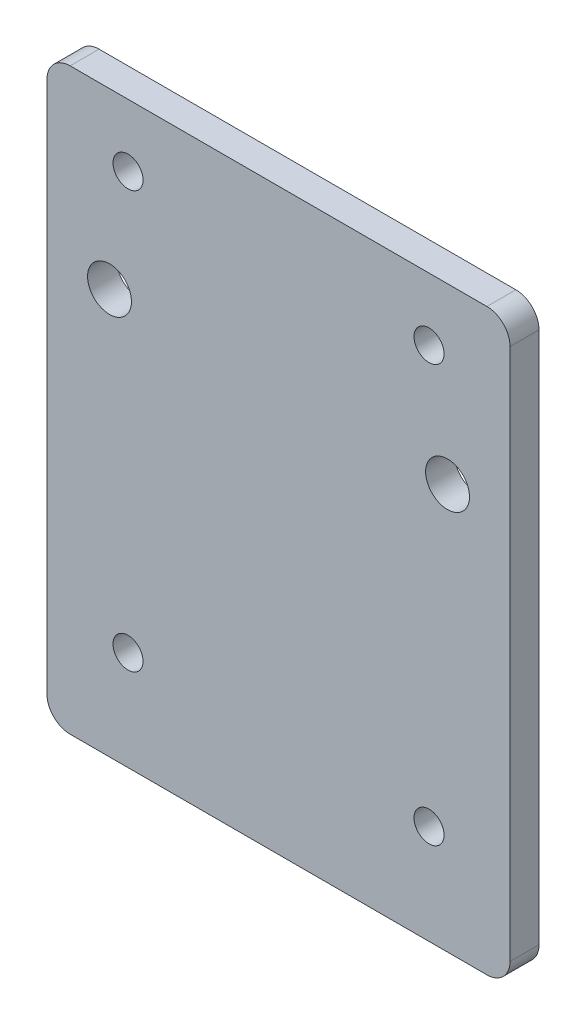
SolidWorks part; units mm, degrees
ref_plane "Front Plane" through (0, 0, 0) normal (0, 0, 1) x (1, 0, 0)
ref_plane "Top Plane" through (0, 0, 0) normal (0, 1, 0) x (1, 0, 0)
ref_plane "Right Plane" through (0, 0, 0) normal (1, 0, 0) x (0, 0, -1)
sketch "Sketch1" plane through (0, 0, 0) normal (0, 0, 1) x (1, 0, 0)
  line L1 (-25.4, 31.75) -> (25.4, 31.75)
  line L2 (-25.4, 31.75) -> (-25.4, -31.75)
  line L3 (-25.4, -31.75) -> (25.4, -31.75)
  line L4 (25.4, 31.75) -> (25.4, -31.75)
  line L5 (-25.4, 31.75) -> (25.4, -31.75) construction
  line L6 (-25.4, -31.75) -> (25.4, 31.75) construction
  point P0 (0, 0)
  dimension "D1" = 63.5
  dimension "D2" = 50.8
extrude "Boss-Extrude1" add sketch "Sketch1" along normal blind 3.175
hole_wizard "#10 (0.1935) Diameter Hole1" positions "Sketch2" profile "Sketch3" hole size "#10" standard "ANSI Inch" end condition up to next
sketch "Sketch2" plane through (0, 0, 0) normal (0, 0, -1) x (-1, 0, 0)
  line L0 (-25.4, -31.75) -> (-25.4, 31.75) construction
  line L1 (-25.4, 31.75) -> (25.4, 31.75) construction
  point P0 (-18.542, 12.7)
  point P2 (18.542, 12.7)
  dimension "D1" = 37.084
  dimension "D2" = 6.858
  dimension "D3" = 19.05
  dimension "D4" = 19.05
sketch "Sketch3" plane through (18.542, 12.7, 0) normal (1, 0, 0) x (0, 1, 0)
  line L0 (0, 0) -> (0, 3.175)
  line L1 (0, 3.175) -> (2.4066, 3.175)
  line L2 (2.4066, 3.175) -> (2.4066, 0)
  line L5 (2.4066, 0) -> (0, 0)
  line L11 (0, -6.35) -> (0, 107.95) construction
  dimension "Thru Hole Dia." = 4.8133
  dimension "Thru Hole Depth" = 3.175
hole_wizard "M3 Clearance Hole1" positions "Sketch4" profile "Sketch5" hole size "M3" standard "ANSI Metric" end condition up to next
sketch "Sketch4" plane through (0, 0, 0) normal (0, 0, -1) x (-1, 0, 0)
  line L1 (16.51, -20.828) -> (-16.51, -20.828)
  line L2 (16.51, -20.828) -> (16.51, 24.892)
  line L3 (16.51, 24.892) -> (-16.51, 24.892)
  line L4 (-16.51, -20.828) -> (-16.51, 24.892)
  line L5 (16.51, -20.828) -> (-16.51, 24.892) construction
  line L6 (16.51, 24.892) -> (-16.51, -20.828) construction
  line L7 (-25.4, 31.75) -> (25.4, 31.75) construction
  line L8 (-25.4, -31.75) -> (-25.4, 31.75) construction
  point P0 (-16.51, 24.892)
  point P2 (16.51, 24.892)
  point P4 (-16.51, -20.828)
  point P6 (16.51, -20.828)
  point P133 (0, 0)
  point P134 (0, 0)
  point P135 (0, 0)
  point P136 (0, 0)
  point P137 (0, 0)
  dimension "D1" = 33.02
  dimension "D2" = 45.72
  dimension "D3" = 6.858
  dimension "D4" = 8.89
sketch "Sketch5" plane through (16.51, 24.892, 0) normal (1, 0, 0) x (0, 1, 0)
  line L0 (0, 0) -> (0, 3.175)
  line L1 (0, 3.175) -> (1.6492, 3.175)
  line L2 (1.6492, 3.175) -> (1.6492, 0)
  line L5 (1.6492, 0) -> (0, 0)
  line L11 (0, -6.35) -> (0, 107.95) construction
  dimension "Thru Hole Dia." = 3.2984
  dimension "Thru Hole Depth" = 3.175
fillet "Fillet1" radius 2.54 4 edges at (25.4, -31.75, 1.5875) (-25.4, -31.75, 1.5875) (-25.4, 31.75, 1.5875) (25.4, 31.75, 1.5875)
